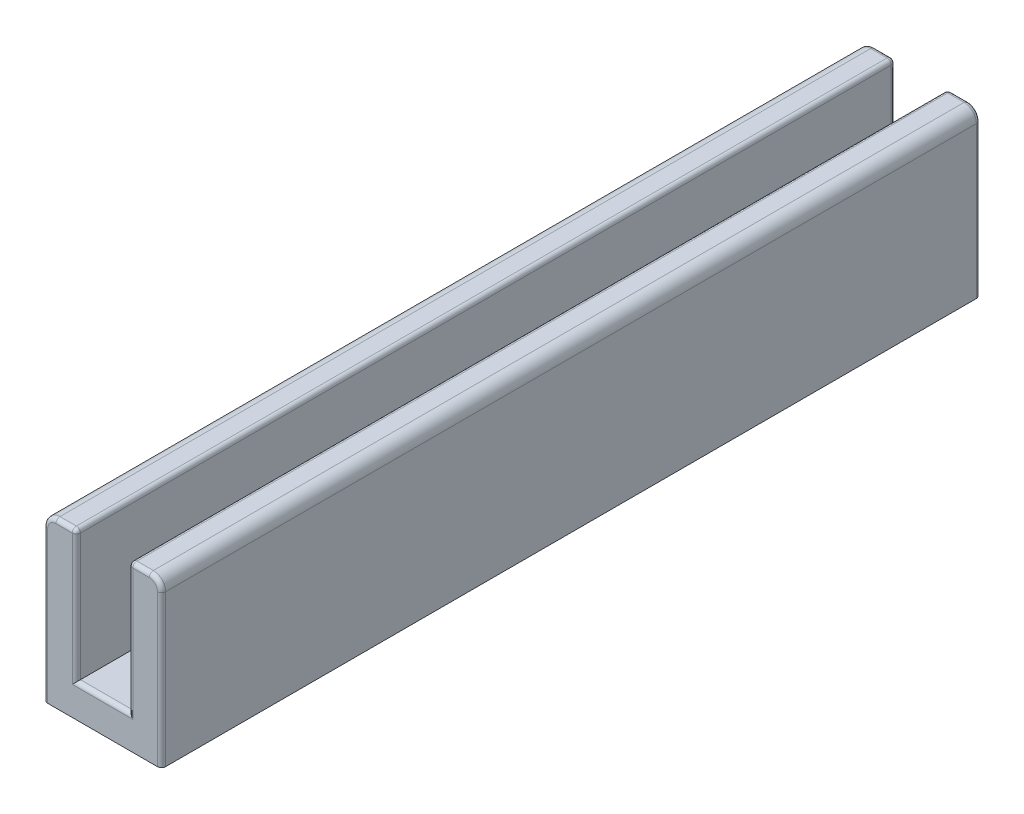
SolidWorks part; units mm, degrees
material "Plastique personnalisé"
ref_plane "Plan de face" through (0, 0, 0) normal (0, 0, 1) x (1, 0, 0)
ref_plane "Plan de dessus" through (0, 0, 0) normal (0, 1, 0) x (1, 0, 0)
ref_plane "Plan de droite" through (0, 0, 0) normal (1, 0, 0) x (0, 0, -1)
sketch "Esquisse1" plane through (0, 0, 0) normal (0, 0, 1) x (1, 0, 0)
  line L0 (3.2, 0) -> (0, 0)
  line L1 (1.6, 0) -> (1.6, -2) construction
  line L2 (3.2, 0) -> (5.2, 0) construction
  line L3 (5.2, 0) -> (5.2, -2)
  line L4 (5.2, -2) -> (-2, -2)
  line L5 (5.2, 0) -> (5.2, 8)
  line L6 (5.2, 8) -> (3.2, 8)
  line L7 (3.2, 8) -> (3.2, 0)
  line L8 (0, 8) -> (0, 0)
  line L9 (-2, 8) -> (0, 8)
  line L10 (-2, 0) -> (-2, 8)
  line L11 (-2, 0) -> (-2, -2)
  dimension "D3" = 2
  dimension "D4" = 8
  dimension "D5" = 2
extrude "Boss.-Extru.1" add sketch "Esquisse1" along normal blind 50
fillet "Congé1" radius 0.75 2 edges at (-2, 8, 25) (5.2, 8, 25)
fillet "Congé2" radius 0.25 2 edges at (0, 8, 25) (3.2, 8, 25)
fillet "Congé3" radius 0.25 22 edges at (0, 3.875, 0) (-0.0732, 7.9268, 0) (-2, 2.625, 0) (-1.7803, 7.7803, 0) (5.2, 2.625, 0) (4.9803, 7.7803, 0) (3.2, 3.875, 0) (3.2732, 7.9268, 0) (0, 3.875, 50) (-0.0732, 7.9268, 50) (-2, 2.625, 50) (-1.7803, 7.7803, 50) (5.2, 2.625, 50) (3.2, 3.875, 50) (3.2732, 7.9268, 50) (3.95, 8, 50) (1.6, 0, 0) (-0.75, 8, 0) (3.95, 8, 0) (-0.75, 8, 50) (1.6, 0, 50) (4.9803, 7.7803, 50)
